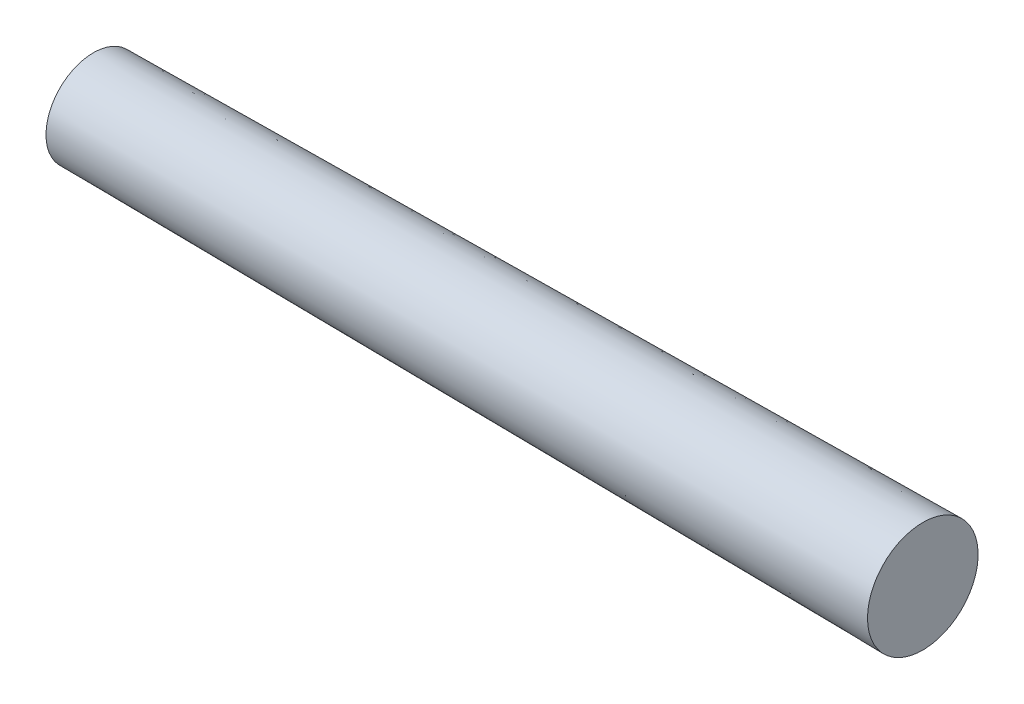
SolidWorks part; units mm, degrees
ref_plane "Front Plane" through (0, 0, 0) normal (0, 0, 1) x (1, 0, 0)
ref_plane "Top Plane" through (0, 0, 0) normal (0, 1, 0) x (1, 0, 0)
ref_plane "Right Plane" through (0, 0, 0) normal (1, 0, 0) x (0, 0, -1)
sketch "Sketch1" plane through (0, 0, 0) normal (0, 0, 1) x (1, 0, 0)
  line L0 (0, 0) -> (0, 6)
  line L1 (0, 6) -> (105, 7)
  line L2 (105, 7) -> (105, 0)
  line L3 (0, 0) -> (121.5557, 0) construction
  line L4 (0, 0) -> (105, 0)
  point P7 (53.7319, 0)
  point P8 (1.1201, 0)
  dimension "D1" = 6
  dimension "D2" = 7
  dimension "D3" = 105
revolve "Revolve1" add sketch "Sketch1" angle 360 about L3
